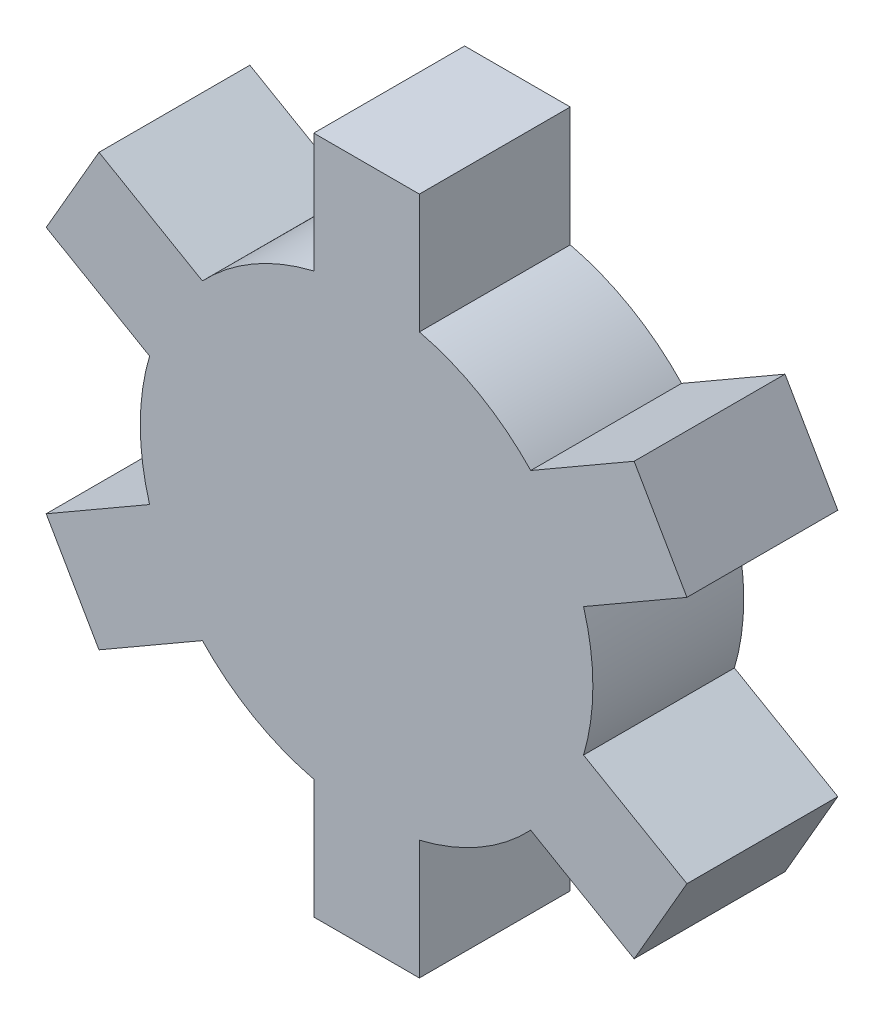
SolidWorks part; units mm, degrees
ref_plane "Front Plane" through (0, 0, 0) normal (0, 0, 1) x (1, 0, 0)
ref_plane "Top Plane" through (0, 0, 0) normal (0, 1, 0) x (1, 0, 0)
ref_plane "Right Plane" through (0, 0, 0) normal (1, 0, 0) x (0, 0, -1)
sketch "Sketch1" plane through (0, 0, 0) normal (0, 0, 1) x (1, 0, 0)
  circle A0 centre (0, 0) radius 15
  dimension "D1" = 30
extrude "Boss-Extrude1" add sketch "Sketch1" along normal blind 10
sketch "Sketch2" plane through (0, 0, 10) normal (0, 0, 1) x (1, 0, 0)
  line L0 (-3.5, 7.5) -> (-3.5, 22.5)
  line L1 (-3.5, 7.5) -> (3.5, 7.5)
  line L2 (-3.5, 22.5) -> (3.5, 22.5)
  line L3 (3.5, 7.5) -> (3.5, 22.5)
  line L4 (-3.5, 7.5) -> (3.5, 22.5) construction
  line L5 (-3.5, 22.5) -> (3.5, 7.5) construction
  circle A0 centre (0, 0) radius 15 construction
  point P1 (0, 15)
  dimension "D1" = 7
  dimension "D2" = 22.5
extrude "Boss-Extrude2" add sketch "Sketch2" against normal up to surface (10 mm away) up to face at (15, 0, 0)
pattern_circular "CirPattern1" count 6 over 360 about axis through (0, 0, 0) along (0, 0, 1) of "Boss-Extrude2"
